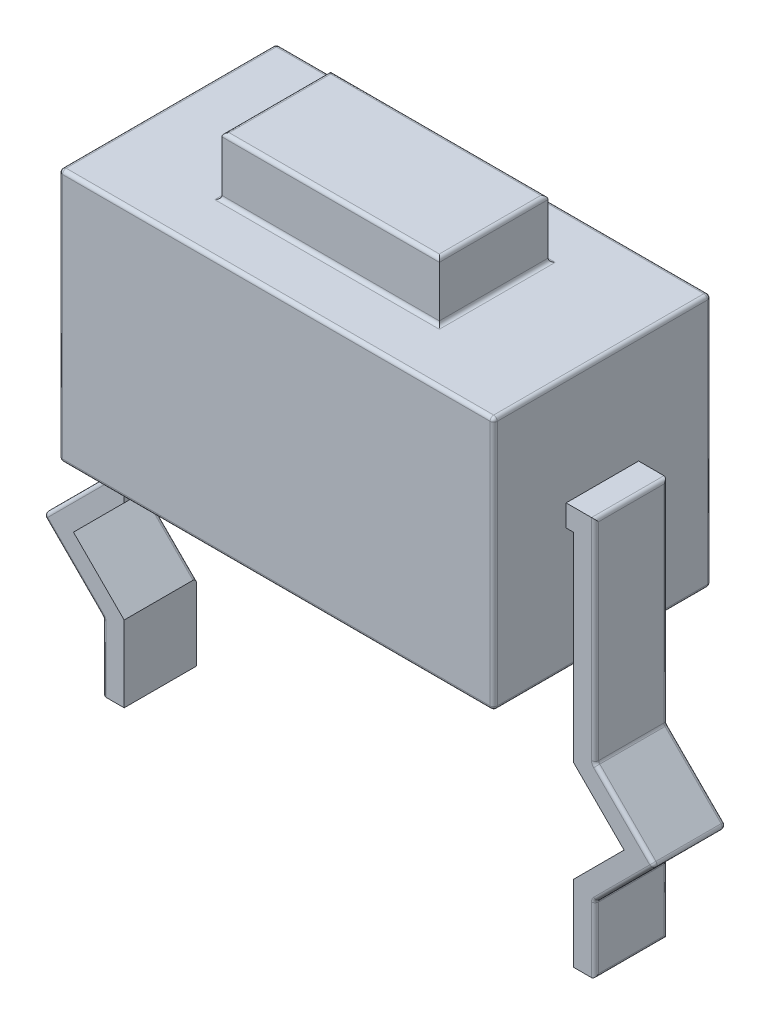
SolidWorks part; units mm, degrees
ref_plane "Front Plane" through (0, 0, 0) normal (0, 0, 1) x (1, 0, 0)
ref_plane "Top Plane" through (0, 0, 0) normal (0, 1, 0) x (1, 0, 0)
ref_plane "Right Plane" through (0, 0, 0) normal (1, 0, 0) x (0, 0, -1)
sketch "Sketch1" plane through (0, 0, 0) normal (0, 1, 0) x (1, 0, 0)
  line L1 (0, 0) -> (6, 0)
  line L2 (0, 0) -> (0, 3)
  line L3 (0, 3) -> (6, 3)
  line L4 (6, 0) -> (6, 3)
  dimension "D1" = 3
  dimension "D2" = 6
extrude "Boss-Extrude1" add sketch "Sketch1" along normal blind 3.5
ref_plane "Plane1" through (0, 0, -1.5) normal (0, 0, 1) x (1, 0, 0)
sketch "Sketch2" plane through (0, 0, -1.5) normal (0, 0, 1) x (1, 0, 0)
  line L0 (0, 1.7) -> (-0.1, 1.7)
  line L1 (-0.1, 1.7) -> (-0.1, -0.7227)
  line L2 (0, 2) -> (-0.4, 2)
  line L3 (-0.4, 2) -> (-0.4, -0.9257)
  line L4 (0, 0) -> (6, 0)
  line L5 (6, 0) -> (6, 3.5)
  line L6 (6, 3.5) -> (0, 3.5)
  line L7 (0, 3.5) -> (0, 0)
  line L8 (0, 0) -> (6, 0)
  line L9 (6, 0) -> (6, 3.5)
  line L10 (6, 3.5) -> (0, 3.5)
  line L11 (0, 3.5) -> (0, 0)
  line L12 (-0.4, -0.9257) -> (-1.2243, -1.75)
  line L13 (-1.2243, -1.75) -> (-0.4, -2.5743)
  line L14 (-0.1, -0.7227) -> (-0.1, -1.05)
  line L15 (-0.1, -1.05) -> (-0.8, -1.75)
  line L16 (-0.8, -1.75) -> (-0.1, -2.45)
  line L17 (-0.1, -2.45) -> (-0.1, -3.5)
  line L18 (-0.4, -2.5743) -> (-0.4, -3.5)
  line L19 (-0.4, -3.5) -> (-0.1, -3.5)
  point P16 (0, 0)
  point P18 (0, 0)
  point P19 (-0.7673, -2.2538)
  dimension "D2" = 0.3
  dimension "D4" = 0.1
  dimension "D3" = 0.3
  dimension "D5" = 1.5
  dimension "D6" = 0.3
  dimension "D9" = 3.5
  dimension "D7" = 0.3
  dimension "D8" = 1.75
  dimension "D10" = 135
  dimension "D11" = 0.7
  dimension "D1" = 0
extrude "Boss-Extrude2" add sketch "Sketch2" along normal blind 0.5 and the other way blind 0.5 contours L18 L19 L17 L16 L15 L14 L1 L0 L11 L2 L3 L12 L13
ref_plane "Plane2" through (3, 0, 0) normal (-1, 0, 0) x (0, 0, 1)
mirror "Mirror1" about plane through (3, 0, 0) normal (-1, 0, 0) of "Boss-Extrude2"
sketch "Sketch3" plane through (0, 3.5, 0) normal (0, 1, 0) x (1, 0, 0)
  line L0 (6, 3) -> (0, 3) construction
  line L1 (1.5, 2.25) -> (4.5, 2.25)
  line L2 (1.5, 2.25) -> (1.5, 0.75)
  line L3 (1.5, 0.75) -> (4.5, 0.75)
  line L4 (4.5, 2.25) -> (4.5, 0.75)
  line L5 (1.5, 2.25) -> (4.5, 0.75) construction
  line L6 (1.5, 0.75) -> (4.5, 2.25) construction
  line L7 (0, 0) -> (6, 0) construction
  line L8 (0, 3) -> (0, 0) construction
  line L9 (6, 0) -> (6, 3) construction
  point P0 (3, 1.5)
  point P5 (3, 0)
  point P6 (3, 3)
  point P7 (0, 1.5)
  point P12 (6, 1.5)
  point P15 (3, 1.5)
  dimension "D1" = 3
  dimension "D2" = 1.5
extrude "Boss-Extrude3" add sketch "Sketch3" along normal blind 0.8
fillet "Fillet1" radius 0.05 51 edges at (3, 0, 0) (6, 1.75, 0) (6, 0, -1.5) (3, 3.5, -2.25) (1.5, 3.5, -1.5) (3, 3.5, -0.75) (4.5, 3.5, -1.5) (6, 3.5, -1.5) (3, 3.5, 0) (6, 1.75, -3) (3, 3.5, -3) (3, 0, -3) (-0.8121, -2.1621, -2) (-0.8121, -2.1621, -1) (-0.4, -3.0371, -2) (-0.4, -2.5743, -1.5) (-0.4, -3.0371, -1) (-0.4, -3.5, -1.5) (-0.8121, -1.3379, -2) (-0.8121, -1.3379, -1) (-1.2243, -1.75, -1.5) (-0.4, 0.5371, -2) (-0.4, 2, -1.5) (-0.4, 0.5371, -1) (-0.4, -0.9257, -1.5) (6.4, -3.0371, -2) (6.4, -3.5, -1.5) (6.4, -3.0371, -1) (6.8121, -1.3379, -2) (6.8121, -1.3379, -1) (6.8121, -2.1621, -2) (6.4, -2.5743, -1.5) (6.8121, -2.1621, -1) (7.2243, -1.75, -1.5) (6.4, 0.5371, -2) (6.4, -0.9257, -1.5) (6.4, 0.5371, -1) (6.4, 2, -1.5) (3, 4.3, -0.75) (1.5, 4.3, -1.5) (3, 4.3, -2.25) (4.5, 4.3, -1.5) (0, 1.7, -1.5) (0, 1.85, -1) (0, 2, -1.5) (0, 1.85, -2) (0, 1.75, -3) (0, 3.5, -1.5) (0, 1.75, 0) (0, 0, -1.5) (-0.45, -2.1, -2)
equation "\"D3@Sketch2\"=\"D2@Sketch2\""
equation "\"D6@Sketch2\"=\"D2@Sketch2\""
equation "\"D7@Sketch2\"=\"D2@Sketch2\""
equation "\"D8@Sketch2\"=\"D9@Sketch2\"/2"
